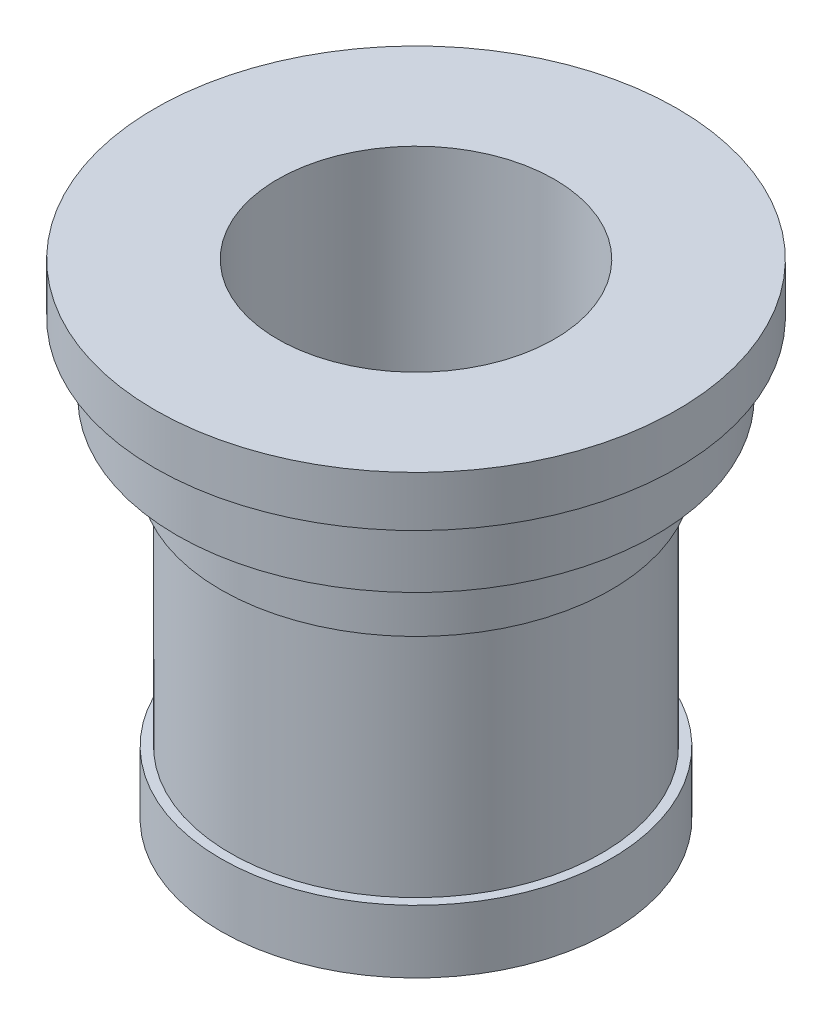
SolidWorks part; units mm, degrees
ref_plane "Front Plane" through (0, 0, 0) normal (0, 0, 1) x (1, 0, 0)
ref_plane "Top Plane" through (0, 0, 0) normal (0, 1, 0) x (1, 0, 0)
ref_plane "Right Plane" through (0, 0, 0) normal (1, 0, 0) x (0, 0, -1)
sketch "Sketch1" plane through (0, 0, 0) normal (0, 0, 1) x (1, 0, 0)
  line L0 (0, 0) -> (0, 89.5013) construction
  line L1 (22, 0) -> (31, 0)
  line L2 (31, 0) -> (31, 10)
  line L3 (31, 10) -> (29.5, 10)
  line L4 (29.5, 10) -> (29.5, 47)
  line L5 (29.5, 47) -> (31, 47)
  line L6 (31, 47) -> (31, 58)
  line L7 (31, 58) -> (38, 58)
  line L8 (38, 58) -> (38, 69)
  line L9 (38, 69) -> (41.5, 69)
  line L10 (41.5, 69) -> (41.5, 77)
  line L11 (41.5, 77) -> (22, 77)
  line L13 (22, 77) -> (22, 0)
  dimension "D1" = 10
  dimension "D2" = 37
  dimension "D3" = 11
  dimension "D4" = 11
  dimension "D5" = 8
  dimension "D6" = 83
  dimension "D7" = 59
  dimension "D8" = 62
  dimension "D9" = 76
  dimension "D10" = 62
  dimension "D11" = 44
revolve "Revolve1" add sketch "Sketch1" angle 360 about L0
